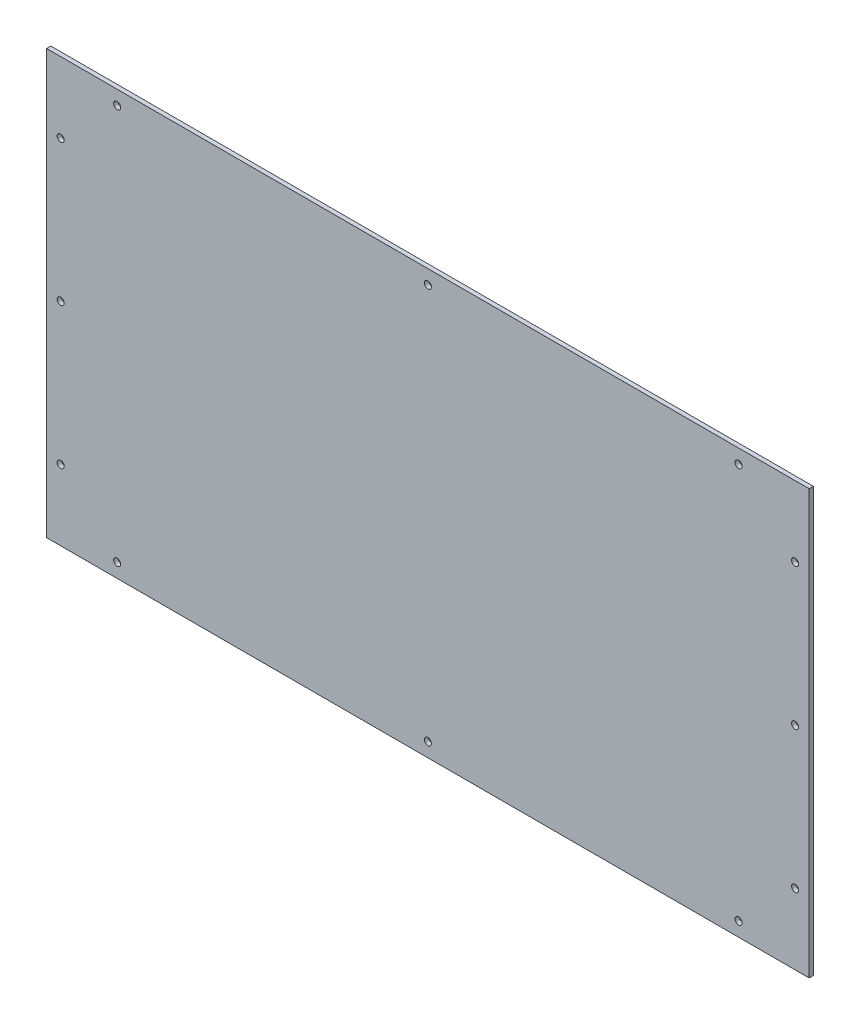
SolidWorks part; units mm, degrees
ref_plane "Alzado" through (0, 0, 0) normal (0, 0, 1) x (1, 0, 0)
ref_plane "Planta" through (0, 0, 0) normal (0, 1, 0) x (1, 0, 0)
ref_plane "Vista lateral" through (0, 0, 0) normal (1, 0, 0) x (0, 0, -1)
sketch "Croquis1" plane through (0, 0, 0) normal (0, 0, 1) x (1, 0, 0)
  line L1 (-270, 150) -> (270, 150)
  line L2 (-270, 150) -> (-270, -150)
  line L3 (-270, -150) -> (270, -150)
  line L4 (270, 150) -> (270, -150)
  line L5 (-270, 150) -> (270, -150) construction
  line L6 (-270, -150) -> (270, 150) construction
  point P0 (0, 0)
  dimension "D1" = 540
  dimension "D2" = 300
extrude "Saliente-Extruir1" add sketch "Croquis1" along normal blind 3
sketch "Croquis2" plane through (0, 0, 3) normal (0, 0, 1) x (1, 0, 0)
  line L0 (-270, 150) -> (-270, -150) construction
  line L1 (-260, -140) -> (260, -140) construction
  line L2 (-260, -140) -> (-260, 140) construction
  line L3 (-260, 140) -> (260, 140) construction
  line L4 (260, -140) -> (260, 140) construction
  line L5 (-260, -140) -> (260, 140) construction
  line L6 (-260, 140) -> (260, -140) construction
  line L7 (270, 150) -> (-270, 150) construction
  line L8 (-260, 0) -> (260, 0) construction
  line L9 (0, 140) -> (0, -140) construction
  circle A0 centre (0, 140) radius 2.5
  circle A1 centre (-220, 140) radius 2.5
  circle A2 centre (-260, 0) radius 2.5
  circle A3 centre (-260, 100) radius 2.5
  circle A4 centre (-260, -100) radius 2.5
  circle A5 centre (220, 140) radius 2.5
  circle A6 centre (260, -100) radius 2.5
  circle A7 centre (260, 0) radius 2.5
  circle A8 centre (260, 100) radius 2.5
  circle A9 centre (220, -140) radius 2.5
  circle A10 centre (0, -140) radius 2.5
  circle A11 centre (-220, -140) radius 2.5
  point P0 (0, 0)
  dimension "D3" = 5
  dimension "D5" = 220
  dimension "D7" = 100
  dimension "D1" = 10
  dimension "D2" = 10
  dimension "D4" = 2
  dimension "D6" = 2
extrude "Cortar-Extruir1" cut sketch "Croquis2" against normal through all
